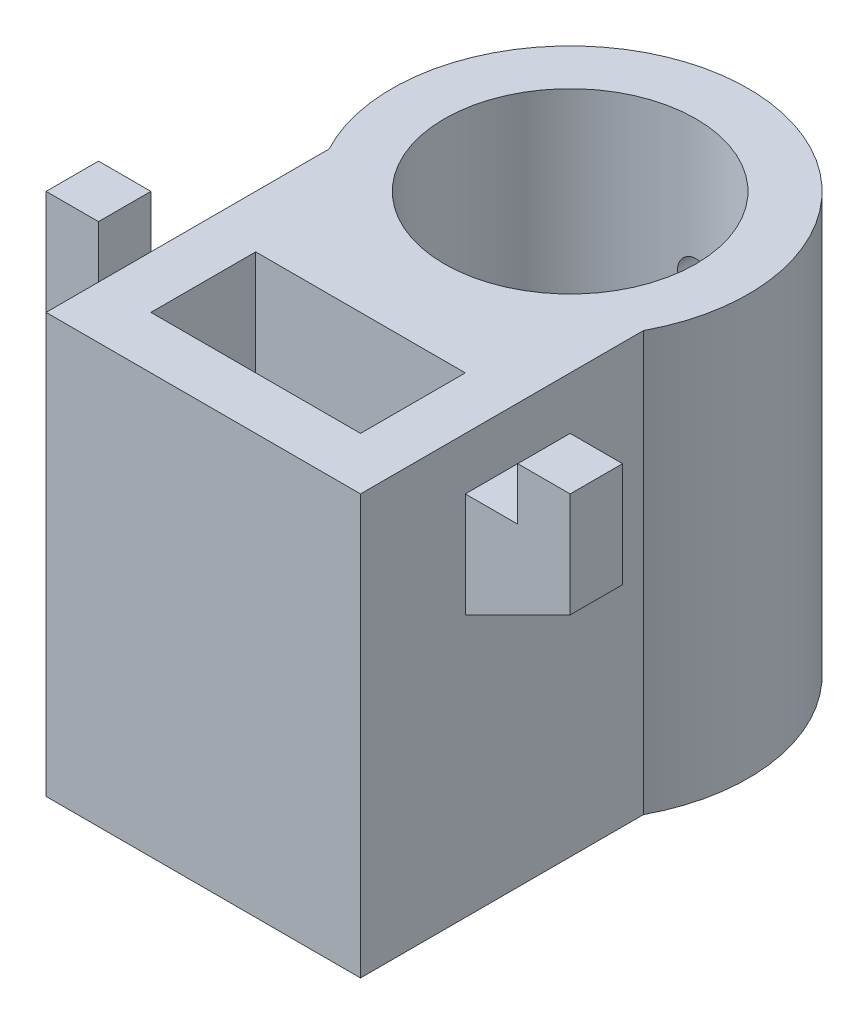
SolidWorks part; units mm, degrees
ref_plane "Front Plane" through (0, 0, 0) normal (0, 0, 1) x (1, 0, 0)
ref_plane "Top Plane" through (0, 0, 0) normal (0, 1, 0) x (1, 0, 0)
ref_plane "Right Plane" through (0, 0, 0) normal (1, 0, 0) x (0, 0, -1)
sketch "Sketch1" plane through (0, 0, 0) normal (0, 1, 0) x (1, 0, 0)
  line L1 (-6.35, -19.05) -> (6.35, -19.05)
  line L2 (-6.35, -19.05) -> (-6.35, -12.7)
  line L3 (-6.35, -12.7) -> (6.35, -12.7)
  line L4 (6.35, -19.05) -> (6.35, -12.7)
  line L7 (-9.525, -22.225) -> (9.525, -22.225)
  line L8 (-9.525, -22.225) -> (-9.525, -5.08)
  line L10 (9.525, -22.225) -> (9.525, -5.08)
  circle A0 centre (0, 0) radius 7.62
  arc A1 (9.525, -5.08) -> (-9.525, -5.08) centre (0, 0) ccw
  point P3 (0, -12.7)
  point P8 (0, -22.225)
  dimension "D5" = 3.175
  dimension "D6" = 3.175
  dimension "D3" = 15.24
  dimension "D7" = 12.7
  dimension "D1" = 6.35
  dimension "D2" = 12.7
  dimension "D4" = 3.175
extrude "Boss-Extrude1" add sketch "Sketch1" along normal blind 25.4
ref_plane "Plane1" through (0, 0, 0) normal (1, 0, 0) x (0, 0, -1)
ref_plane "Plane2" through (0, 0, 15.875) normal (0, 0, -1) x (-1, 0, 0)
sketch "Sketch3" plane through (0, 0, 15.875) normal (0, 0, -1) x (-1, 0, 0)
  line L0 (9.525, 25.4) -> (-9.525, 25.4) construction
  line L1 (-9.525, 22.225) -> (-9.525, 15.875)
  line L2 (-12.7, 22.225) -> (-12.7, 25.4)
  line L3 (-12.7, 25.4) -> (-15.875, 25.4)
  line L4 (-15.875, 19.05) -> (-15.875, 25.4)
  line L5 (-12.7, 22.225) -> (-9.525, 22.225)
  line L6 (-15.875, 19.05) -> (-9.525, 15.875)
  line L7 (-9.525, 25.4) -> (-9.525, 0) construction
  dimension "D1" = 3.175
  dimension "D2" = 3.175
  dimension "D3" = 3.175
  dimension "D4" = 3.175
  dimension "D5" = 6.35
extrude "Boss-Extrude2" add sketch "Sketch3" along normal blind 3.175
mirror "Mirror1" about plane through (0, 0, 0) normal (1, 0, 0) of "Boss-Extrude2"
ref_plane "Plane3" through (0, 0, -10.795) normal (0, 0, -1) x (-1, 0, 0)
sketch "Sketch4" plane through (0, 0, -10.795) normal (0, 0, -1) x (-1, 0, 0)
  line L2 (0, 25.4) -> (0, 0) construction
  line L3 (-10.795, 0) -> (10.795, 0) construction
  line L4 (10.795, 25.4) -> (-10.795, 25.4) construction
  circle A0 centre (0, 8.382) radius 1.0414
  circle A1 centre (0, 17.018) radius 1.0414
  dimension "D1" = 2.0828
  dimension "D3" = 2.0828
  dimension "D2" = 8.382
  dimension "D4" = 8.382
extrude "Cut-Extrude1" cut sketch "Sketch4" against normal up to next
